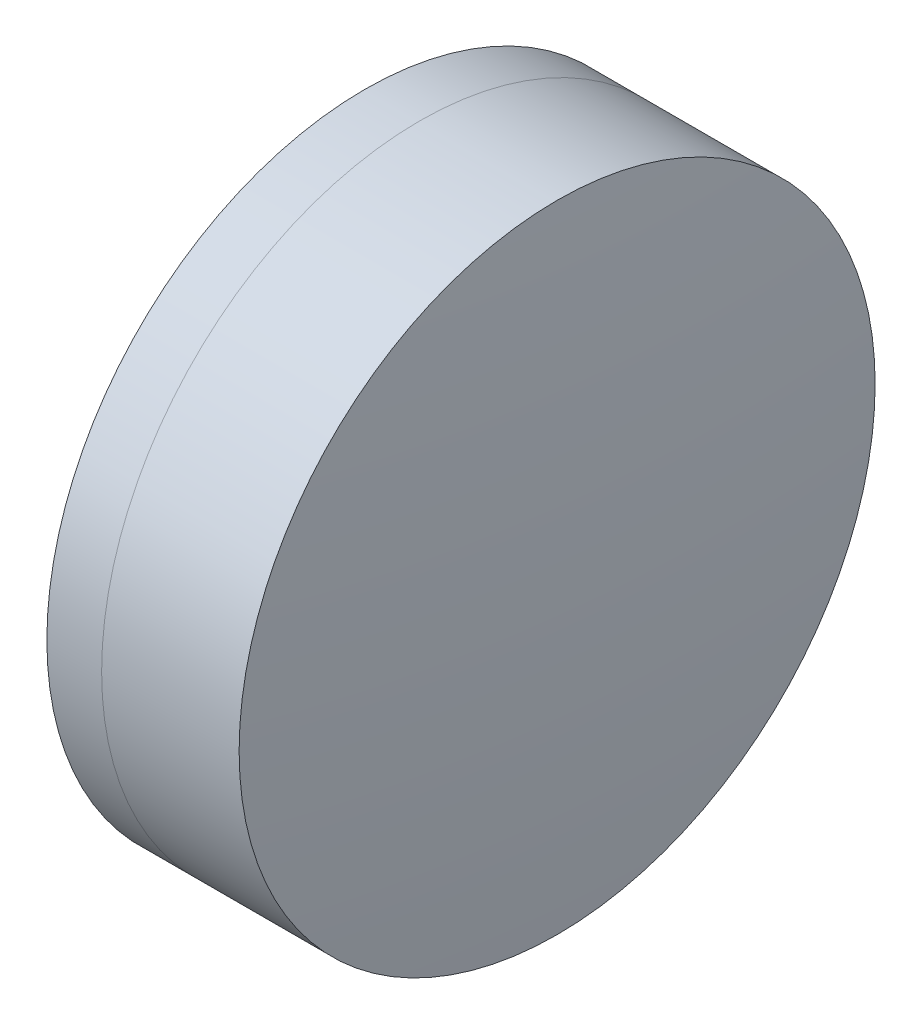
SolidWorks part; units mm, degrees
ref_plane "前视基准面" through (0, 0, 0) normal (0, 0, 1) x (1, 0, 0)
ref_plane "上视基准面" through (0, 0, 0) normal (0, 1, 0) x (1, 0, 0)
ref_plane "右视基准面" through (0, 0, 0) normal (1, 0, 0) x (0, 0, -1)
sketch "草图1" plane through (0, 0, 0) normal (0, 1, 0) x (1, 0, 0)
  line L0 (-0.8161, 0) -> (30.8676, 0) construction
  line L1 (22.9808, -12.7) -> (25.1676, -12.7)
  line L2 (22.9808, 12.7) -> (25.1676, 12.7)
  arc A0 (25.1676, -12.7) -> (25.1676, 12.7) centre (8.3302, 0) ccw
  arc A1 (22.9808, 12.7) -> (22.9808, -12.7) centre (43.8502, 0) ccw
  point P4 (30.8676, 0)
  point P10 (19.4202, 0)
  point P11 (29.4202, 0)
  dimension "D3" = 24.43
  dimension "D4" = 21.09
  dimension "D1" = 12.7
  dimension "D2" = 12.7
  dimension "D5" = 10
revolve "旋转1" add sketch "草图1" angle 360 about L0
sketch "草图2" plane through (0, 0, 0) normal (0, 1, 0) x (1, 0, 0)
  line L0 (-0.5519, 0) -> (34.9089, 0) construction
  line L2 (25.1676, 12.7) -> (30.6588, 12.7)
  line L3 (25.1676, -12.7) -> (30.6588, -12.7)
  arc A0 (30.6588, -12.7) -> (30.6588, 12.7) centre (-112.6998, 0) ccw
  arc A1 (25.1676, -12.7) -> (25.1676, 12.7) centre (8.3302, 0) ccw construction
  arc A2 (25.1676, -12.7) -> (25.1676, 12.7) centre (8.3302, 0) ccw
  point P4 (29.4202, 0)
  point P12 (31.2202, 0)
  dimension "D1" = 143.92
  dimension "D2" = 1.8
revolve "旋转2" add sketch "草图2" angle 360 about L0
